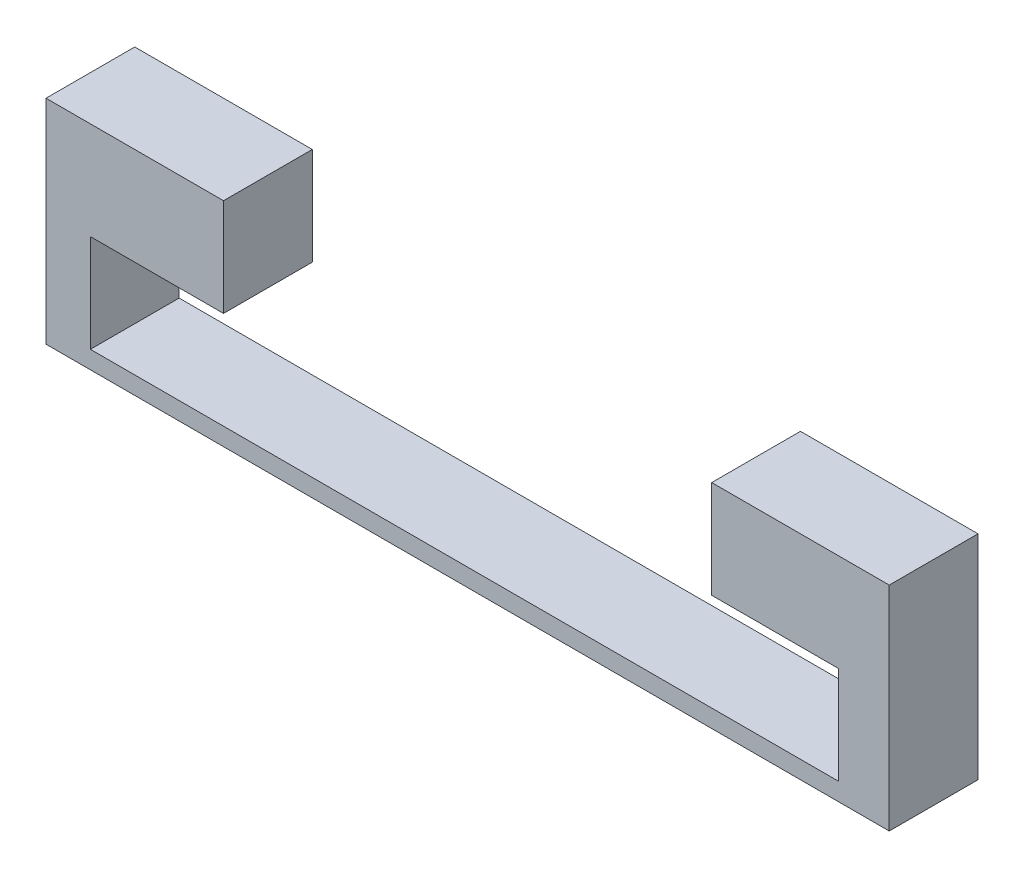
SolidWorks part; units mm, degrees
ref_plane "Front Plane" through (0, 0, 0) normal (0, 0, 1) x (1, 0, 0)
ref_plane "Top Plane" through (0, 0, 0) normal (0, 1, 0) x (1, 0, 0)
ref_plane "Right Plane" through (0, 0, 0) normal (1, 0, 0) x (0, 0, -1)
sketch "Sketch1" plane through (0, 0, 0) normal (0, 0, 1) x (1, 0, 0)
  line L0 (0, 0) -> (19, 0)
  line L1 (19, 0) -> (19, 4.8)
  line L2 (19, 4.8) -> (15, 4.8)
  line L3 (15, 4.8) -> (15, 2.6)
  line L4 (15, 2.6) -> (17.8556, 2.6)
  line L5 (17.8556, 2.6) -> (17.8556, 0.4)
  line L6 (1, 0.4) -> (1, 2.6)
  line L7 (4, 2.6) -> (4, 4.8)
  line L8 (4, 4.8) -> (0, 4.8)
  line L9 (0, 4.8) -> (0, 0)
  line L10 (1, 0.4) -> (17.8556, 0.4)
  line L11 (1, 2.6) -> (4, 2.6)
  dimension "D1" = 19
  dimension "D2" = 4.8
  dimension "D3" = 4.8
  dimension "D4" = 4
  dimension "D5" = 4
  dimension "D6" = 1
  dimension "D7" = 0.4
  dimension "D8" = 2.2
  dimension "D9" = 2.2
extrude "Boss-Extrude1" add sketch "Sketch1" along normal blind 2
